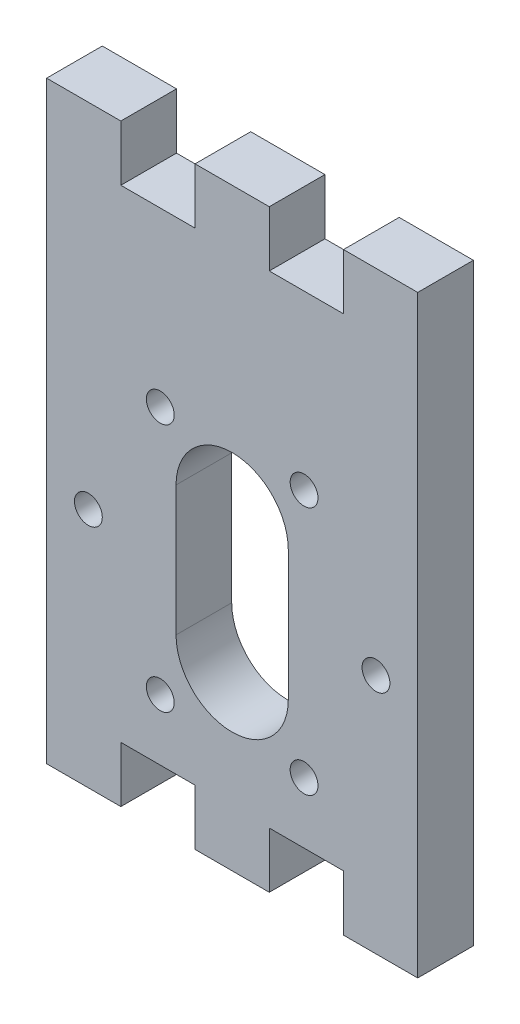
SolidWorks part; units mm, degrees
ref_plane "Plan de face" through (0, 0, 0) normal (0, 0, 1) x (1, 0, 0)
ref_plane "Plan de dessus" through (0, 0, 0) normal (0, 1, 0) x (1, 0, 0)
ref_plane "Plan de droite" through (0, 0, 0) normal (1, 0, 0) x (0, 0, -1)
sketch "Esquisse1" plane through (0, 0, 0) normal (0, 0, 1) x (1, 0, 0)
  line L0 (-6.05, 27) -> (-6.05, 13)
  line L1 (-20, 58) -> (-12, 58)
  line L2 (-20, -6) -> (-20, 58)
  line L3 (-12, 0) -> (-4, 0)
  line L4 (20, 58) -> (20, -1)
  line L5 (6.05, 13) -> (6.05, 27)
  line L6 (4, 0) -> (12, 0)
  line L7 (-4, 58) -> (4, 58)
  line L8 (12, 58) -> (20, 58)
  line L9 (-20, -6) -> (-12, -6)
  line L10 (-12, 0) -> (-12, -6)
  line L11 (-12, 58) -> (-12, 52)
  line L12 (20, -1) -> (20, -6)
  line L13 (20, -6) -> (12, -6)
  line L14 (12, 0) -> (12, -6)
  line L15 (-12, 52) -> (-4, 52)
  line L16 (4, 0) -> (4, -6)
  line L17 (4, -6) -> (-4, -6)
  line L18 (-4, 0) -> (-4, -6)
  line L19 (-4, 58) -> (-4, 52)
  line L21 (4, 58) -> (4, 52)
  line L22 (4, 52) -> (12, 52)
  line L23 (12, 58) -> (12, 52)
  arc A0 (-6.05, 13) -> (6.05, 13) centre (0, 13) ccw
  circle A1 centre (0, 20) radius 15.5 construction
  circle A2 centre (-15.5, 20) radius 1.5
  circle A3 centre (-7.75, 33.4234) radius 1.5
  circle A4 centre (7.75, 33.4234) radius 1.5
  circle A5 centre (15.5, 20) radius 1.5
  circle A6 centre (7.75, 6.5766) radius 1.5
  circle A7 centre (-7.75, 6.5766) radius 1.5
  arc A8 (6.05, 27) -> (-6.05, 27) centre (0, 27) ccw
  point P8 (0, 20)
  point P26 (0, 20)
  dimension "D4" = 12.1
  dimension "D7" = 31
  dimension "D8" = 3
  dimension "D10" = 12.1
  dimension "D2" = 40
  dimension "D3" = 8
  dimension "D5" = 13
  dimension "D6" = 7
  dimension "D11" = 7
  dimension "D12" = 64
  dimension "D13" = 8
  dimension "D14" = 8
  dimension "D15" = 5
  dimension "D16" = 6
  dimension "D17" = 4
  dimension "D18" = 8
  dimension "D19" = 8
  dimension "D20" = 8
  dimension "D21" = 6
  dimension "D22" = 4
  dimension "D9" = 6
extrude "Boss.-Extru.1" add sketch "Esquisse1" along normal blind 6
